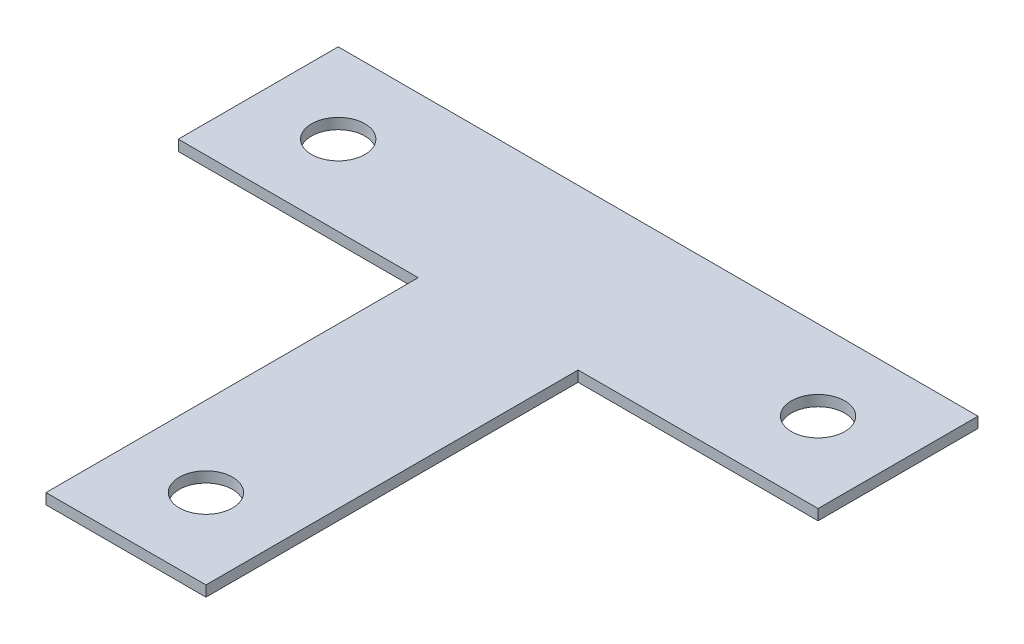
SolidWorks part; units mm, degrees
material "Galvanized Steel"
ref_plane "Front Plane" through (0, 0, 0) normal (0, 0, 1) x (1, 0, 0)
ref_plane "Top Plane" through (0, 0, 0) normal (0, 1, 0) x (1, 0, 0)
ref_plane "Right Plane" through (0, 0, 0) normal (1, 0, 0) x (0, 0, -1)
sketch "Sketch1" plane through (0, 0, 0) normal (0, 1, 0) x (1, 0, 0)
  line L0 (-76.2, 25.1581) -> (76.2, 25.1581) construction
  line L1 (0, -63.5) -> (0, 63.5) construction
  line L2 (-76.2, 25.1581) -> (-19.05, 25.1581)
  line L3 (-19.05, 25.1581) -> (-19.05, -63.5)
  line L4 (-19.05, -63.5) -> (19.05, -63.5)
  line L5 (19.05, -63.5) -> (19.05, 25.1581)
  line L6 (19.05, 25.1581) -> (76.2, 25.1581)
  line L7 (76.2, 25.1581) -> (76.2, 63.2581)
  line L8 (76.2, 63.2581) -> (-76.2, 63.2581)
  line L9 (-76.2, 63.2581) -> (-76.2, 25.1581)
  line L10 (-76.2, 44.2081) -> (76.2, 44.2081) construction
  circle A0 centre (0, -44.45) radius 6.35
  circle A1 centre (-57.15, 44.2081) radius 6.35
  circle A2 centre (57.15, 44.2081) radius 6.35
  point P3 (0, 25.1581)
  point P4 (0, 0)
  point P8 (0, 0)
  point P20 (0, 44.2081)
  dimension "D7" = 12.7
  dimension "D8" = 12.7
  dimension "D9" = 12.7
  dimension "D1" = 152.4
  dimension "D2" = 127
  dimension "D3" = 152.4
  dimension "D4" = 38.1
  dimension "D5" = 38.1
  dimension "D6" = 19.05
  dimension "D10" = 19.05
  dimension "D11" = 19.05
  dimension "D12" = 19.05
extrude "Boss-Extrude1" add sketch "Sketch1" along normal blind 2.54
